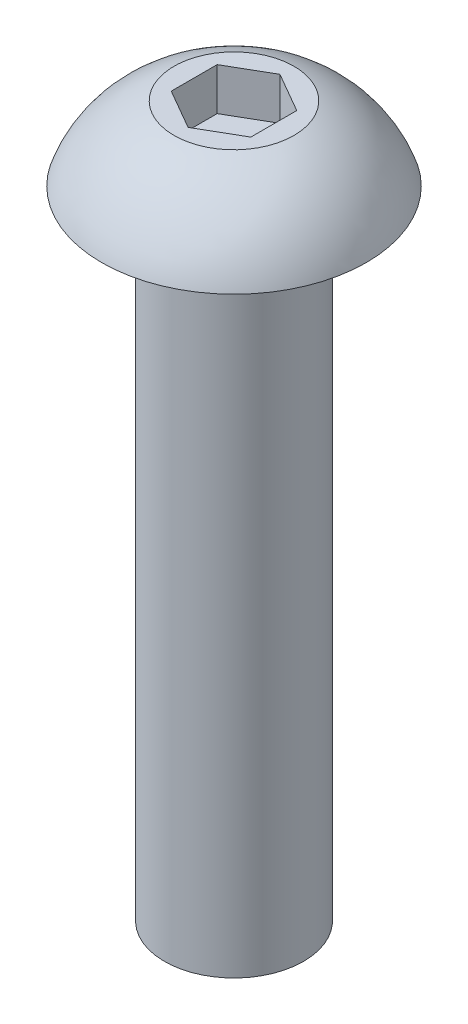
SolidWorks part; units mm, degrees
material "AISI Type 316L stainless steel"
ref_plane "Front Plane" through (0, 0, 0) normal (0, 0, 1) x (1, 0, 0)
ref_plane "Top Plane" through (0, 0, 0) normal (0, 1, 0) x (1, 0, 0)
ref_plane "Right Plane" through (0, 0, 0) normal (1, 0, 0) x (0, 0, -1)
sketch "Sketch1" plane through (0, 0, 0) normal (0, 0, 1) x (1, 0, 0)
  line L0 (-2.0828, 0) -> (-3.9624, 0)
  line L1 (-2.0828, 0) -> (-2.0828, -19.05)
  line L2 (0, -19.05) -> (0, 2.2098)
  line L3 (0, 2.2098) -> (-1.7948, 2.2098)
  line L4 (-2.0828, -19.05) -> (0, -19.05)
  arc A0 (-3.9624, 0) -> (-1.7948, 2.2098) centre (-0.5889, -1.1411) cw
  dimension "D1" = 19.05
  dimension "D2" = 2.2098
  dimension "D3" = 3.9624
  dimension "D4" = 2.0828
  dimension "D5" = 1.7948
revolve "Revolve1" add sketch "Sketch1" angle 360 about L2
sketch "Sketch2" plane through (0, 2.2098, 0) normal (0, 1, 0) x (1, 0, 0)
  line L0 (0, 0) -> (0, 1.3748) construction
  line L1 (-1.1906, 0.6874) -> (-1.1906, -0.6874)
  line L2 (-1.1906, -0.6874) -> (0, -1.3748)
  line L3 (0, -1.3748) -> (1.1906, -0.6874)
  line L4 (1.1906, -0.6874) -> (1.1906, 0.6874)
  line L5 (1.1906, 0.6874) -> (0, 1.3748)
  line L6 (0, 1.3748) -> (-1.1906, 0.6874)
  circle A0 centre (0, 0) radius 1.1906 construction
  dimension "D1" = 2.3813
extrude "Cut-Extrude1" cut sketch "Sketch2" against normal blind 1.27
